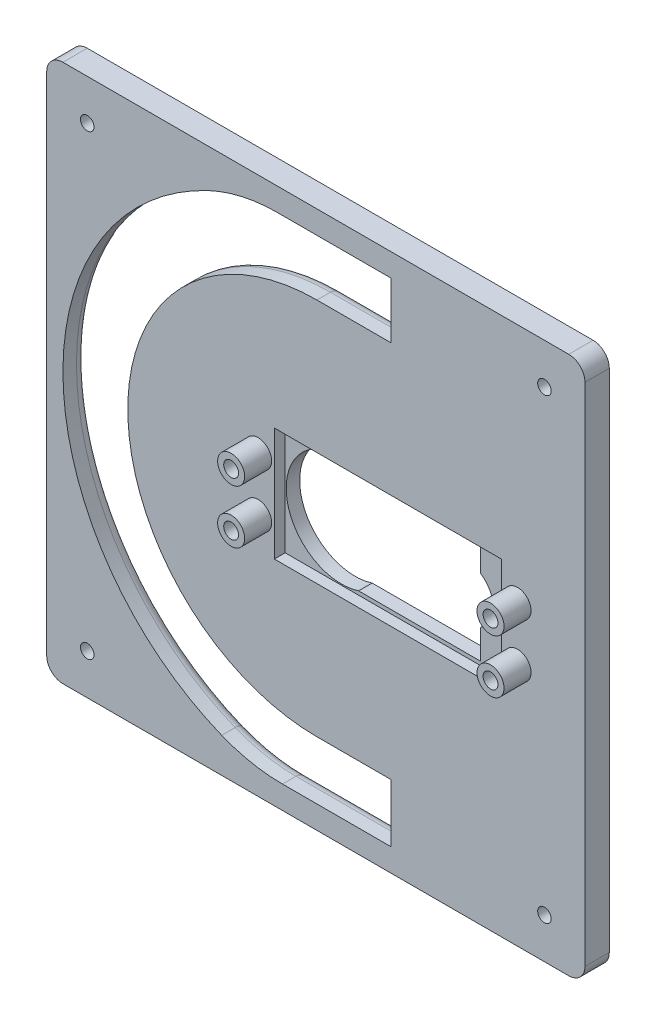
SolidWorks part; units mm, degrees
ref_plane "Front Plane" through (0, 0, 0) normal (0, 0, 1) x (1, 0, 0)
ref_plane "Top Plane" through (0, 0, 0) normal (0, 1, 0) x (1, 0, 0)
ref_plane "Right Plane" through (0, 0, 0) normal (1, 0, 0) x (0, 0, -1)
sketch "Sketch1" plane through (0, 0, 0) normal (0, 0, 1) x (1, 0, 0)
  line L1 (-74.75, 49.6) -> (24.85, 49.6)
  line L2 (-74.75, 49.6) -> (-74.75, -50)
  line L3 (-74.75, -50) -> (24.85, -50)
  line L4 (24.85, 49.6) -> (24.85, -50)
  line L6 (-30.65, 0.0012) -> (-33.35, 0.0012) construction
  line L7 (-15.8956, -0.0011) -> (-5.4456, -0.0011) construction
  circle A0 centre (-22.1047, 0) radius 7.5
  dimension "D3" = 15
  dimension "D8" = 2.7
  dimension "D1" = 99.6
  dimension "D2" = 99.6
  dimension "D5" = 74.75
  dimension "D6" = 50
extrude "Boss-Extrude1" add sketch "Sketch1" along normal blind 3 and the other way blind 1.5
sketch "Sketch20" plane through (0, 0, -1.5) normal (0, 0, -1) x (-1, 0, 0)
  line L0 (-24.85, 49.6) -> (74.75, 49.6) construction
  line L1 (11.0318, 45.36) -> (32.0349, 45.36)
  line L2 (24.75, 35) -> (11.0318, 35)
  line L3 (11.0318, 35) -> (11.0318, 45.36)
  line L4 (11.0318, -45.76) -> (31.1236, -45.76)
  line L5 (24.75, -35) -> (11.0318, -35)
  line L6 (11.0318, -35) -> (11.0318, -45.76)
  line L8 (74.75, -50) -> (-24.85, -50) construction
  arc A0 (42.371, -43.5718) -> (44.8907, 42.4659) centre (24.75, 0) ccw
  arc A1 (24.75, -35) -> (24.75, 35) centre (24.75, 0) ccw
  circle A2 centre (24.75, 0) radius 47 construction
  circle A3 centre (24.75, 0) radius 35 construction
  arc A4 (32.0349, 45.36) -> (44.8907, 42.4659) centre (32.0349, 15.36) cw
  arc A5 (31.1236, -45.76) -> (42.371, -43.5718) centre (31.1236, -15.76) ccw
  dimension "D2" = 24.75
  dimension "D4" = 10.36
  dimension "D6" = 49.6
  dimension "D1" = 35
  dimension "D8" = 30
  dimension "D10" = 30
  dimension "D5" = 10.76
  dimension "D7" = 4.24
  dimension "D9" = 4.24
  dimension "D3" = 12
extrude "Cut-Extrude13" cut sketch "Sketch20" against normal up to surface (4.5 mm away) up to face at (-24.95, -0.2, 3)
sketch "Sketch38" plane through (0, 0, 3) normal (0, 0, 1) x (1, 0, 0)
  line L0 (-22.1047, 0) -> (-36.6047, 0) construction
  circle A0 centre (-35.6241, 5) radius 1.375
  circle A1 centre (-35.6241, -4.9029) radius 1.375
  circle A2 centre (-35.6241, -4.9029) radius 2.5
  circle A3 centre (-35.6241, 5) radius 2.5
  circle A4 centre (12.3759, 5) radius 1.375
  circle A5 centre (12.3759, 5) radius 2.5
  circle A6 centre (12.3759, -4.9029) radius 1.375
  circle A7 centre (12.3759, -4.9029) radius 2.5
  dimension "D1" = 5
  dimension "D3" = 2.75
  dimension "D4" = 2.75
  dimension "D5" = 5
  dimension "D6" = 5
  dimension "D7" = 48
  dimension "D9" = 5
  dimension "D10" = 2.75
  dimension "D11" = 2.75
  dimension "D12" = 5
  dimension "D2" = 5
  dimension "D8" = 48
extrude "Boss-Extrude12" add sketch "Sketch38" along normal blind 5
sketch "Sketch42" plane through (0, 0, -1.5) normal (0, 0, -1) x (-1, 0, 0)
  line L0 (-3.0577, 9.75) -> (19.03, 9.75)
  line L1 (-3.0577, -9.75) -> (19.03, -9.75)
  line L2 (-3.0577, 9.75) -> (-3.0577, 4.2426)
  line L3 (-3.0577, -4.2426) -> (-3.0577, -9.75)
  arc A0 (19.03, -9.75) -> (19.03, 9.75) centre (22.1923, 0) ccw
  arc A1 (-3.0577, 4.2426) -> (-3.0577, -4.2426) centre (0.4423, 0) ccw
  dimension "D2" = 0.4423
  dimension "D3" = 5.5
  dimension "D4" = 9.75
  dimension "D7" = 10.25
  dimension "D1" = 3.0577
  dimension "D5" = 9.75
  dimension "D6" = 19.5
  dimension "D8" = 22.0877
  dimension "D9" = 22.0877
extrude "Cut-Extrude35" cut sketch "Sketch42" against normal blind 10 contours L2 A1 L3 L1 A0 L0
sketch "Sketch43" plane through (0, 0, -1.5) normal (0, 0, -1) x (-1, 0, 0)
  line L0 (-3.0577, -9.75) -> (-3.5577, -9.75)
  line L1 (-3.5577, -9.75) -> (-3.5577, -4.2963)
  line L2 (-3.0577, 9.75) -> (-3.5577, 9.75)
  line L3 (-3.5577, 9.75) -> (-3.5577, 4.2963)
  line L4 (-3.0577, 9.75) -> (-3.0577, 4.5853)
  line L5 (-3.0577, 4.5853) -> (-3.0577, -4.5853)
  line L6 (-3.0577, -4.2426) -> (-3.0577, -9.75) construction
  line L7 (-3.0577, -4.5853) -> (-3.0577, -9.75)
  arc A0 (-3.5577, 4.2963) -> (-3.5577, -4.2963) centre (-0.7407, 0) ccw
  dimension "D1" = 5.1375
  dimension "D2" = 0.7407
  dimension "D5" = 9.75
  dimension "D3" = 0.5
  dimension "D4" = 0.5
  dimension "D6" = 5.1647
  dimension "D7" = 5.1647
extrude "Cut-Extrude36" cut sketch "Sketch43" against normal up to surface (4.5 mm away) up to face at (-6.2069, 0, 3)
sketch "Sketch44" plane through (0, 0, 3) normal (0, 0, 1) x (1, 0, 0)
  circle A0 centre (12.3759, -4.9029) radius 1.5
  circle A1 centre (12.3759, 5) radius 1.5
  circle A2 centre (-35.6241, 5) radius 1.5
  circle A3 centre (-35.6241, -4.9029) radius 1.5
extrude "Cut-Extrude37" cut sketch "Sketch44" against normal blind 3
hole_wizard "M3x0.5 Tapped Hole1" positions "Sketch45" profile "Sketch47" tap size "M3x0.5" standard "ANSI Metric" end condition through all
sketch "Sketch45" plane through (0, 0, -1.5) normal (0, 0, -1) x (-1, 0, 0)
  line L0 (-24.85, -50) -> (-24.85, 49.6) construction
  line L1 (-24.85, 49.6) -> (74.75, 49.6) construction
  line L2 (74.75, 49.6) -> (74.75, -50) construction
  line L3 (74.75, -50) -> (-24.85, -50) construction
  point P0 (-17.35, 42.1)
  point P2 (-17.35, -42.5)
  point P4 (67.25, -42.5)
  point P6 (67.25, 42.1)
  dimension "D1" = 7.5
  dimension "D2" = 7.5
  dimension "D3" = 7.5
  dimension "D4" = 7.5
  dimension "D5" = 7.5
  dimension "D6" = 7.5
  dimension "D7" = 7.5
  dimension "D8" = 7.5
sketch "Sketch47" plane through (17.35, 42.1, -1.5) normal (1, 0, 0) x (0, 1, 0)
  line L0 (0, 0) -> (0, 9.5)
  line L1 (0, 9.5) -> (1.25, 9.5)
  line L2 (1.25, 9.5) -> (1.25, 0)
  line L5 (1.25, 0) -> (0, 0)
  line L11 (0, -6.35) -> (0, 107.95) construction
  dimension "Thru Tap Drill Dia." = 2.5
  dimension "Thru Tap Drill Depth" = 9.5
cosmetic thread "Hole Thread1" parameters "D2"=3
cosmetic thread "Hole Thread2" parameters "D2"=3
cosmetic thread "Hole Thread3" parameters "D2"=3
cosmetic thread "Hole Thread4" parameters "D2"=3
fillet "Fillet1" radius 3 4 edges at (24.85, 49.6, 0.75) (24.85, -50, 0.75) (-74.75, -50, 0.75) (-74.75, 49.6, 0.75)
fillet "Fillet3" radius 2 10 edges at (-17.8909, -35, -1.5) (-59.75, 0, -1.5) (-21.0777, -45.76, -1.5) (-36.8528, -45.2079, -1.5) (-71.7299, -1.3758, -1.5) (-38.6237, 44.6275, -1.5) (-11.0318, -40.38, -1.5) (-17.8909, 35, -1.5) (-11.0318, 40.18, -1.5) (-21.5334, 45.36, -1.5)
sketch "Sketch48" plane through (0, 0, 3) normal (0, 0, 1) x (1, 0, 0)
  line L0 (-35.6241, 5) -> (12.3759, -4.9029) construction
  line L2 (-32.6241, 10.5485) -> (9.3759, 10.5485)
  line L3 (-32.6241, 10.5485) -> (-32.6241, -10.4515)
  line L4 (-32.6241, -10.4515) -> (9.3759, -10.4515)
  line L5 (9.3759, 10.5485) -> (9.3759, -10.4515)
  line L6 (-32.6241, 10.5485) -> (9.3759, -10.4515) construction
  line L7 (-32.6241, -10.4515) -> (9.3759, 10.5485) construction
  point P4 (-11.6241, 0.0485)
  dimension "D1" = 21
  dimension "D2" = 42
extrude "Cut-Extrude38" cut sketch "Sketch48" against normal blind 2
